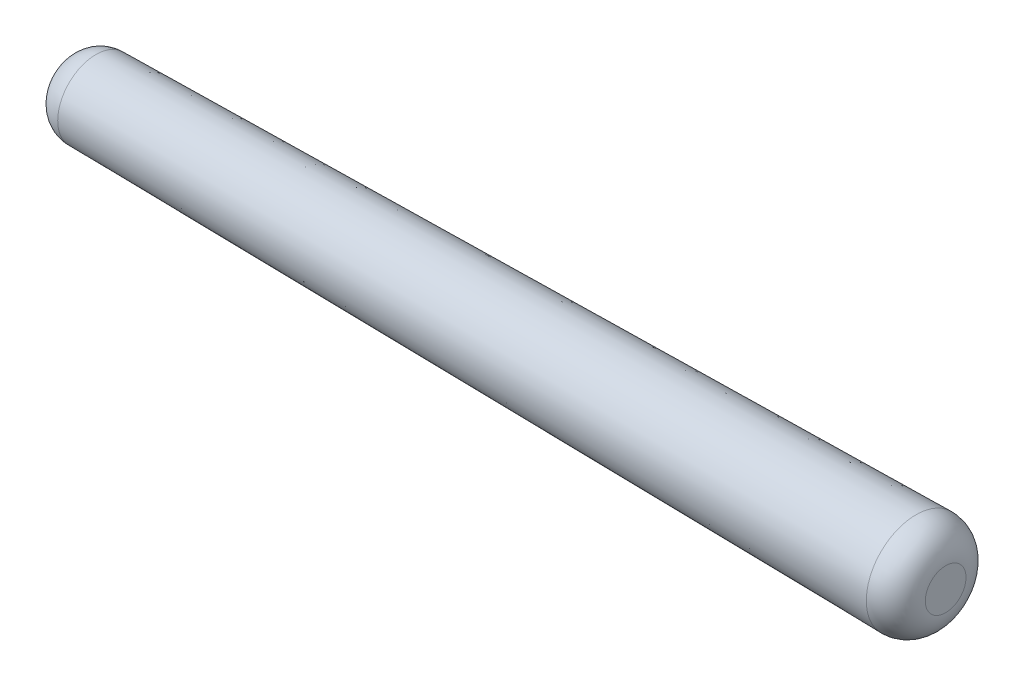
SolidWorks part; units mm, degrees
ref_plane "Front Plane" through (0, 0, 0) normal (0, 0, 1) x (1, 0, 0)
ref_plane "Top Plane" through (0, 0, 0) normal (0, 1, 0) x (1, 0, 0)
ref_plane "Right Plane" through (0, 0, 0) normal (1, 0, 0) x (0, 0, -1)
sketch "Sketch1" plane through (0, 0, 0) normal (1, 0, 0) x (0, 0, -1)
  circle A0 centre (0, 0) radius 0.6
  dimension "D1" = 1.2
sketch "Sketch2" plane through (0, 0, 0) normal (0, 0, 1) x (1, 0, 0)
  line L0 (6, 0) -> (-6, 0)
  line L1 (-6, -0.5162) -> (6, -0.6838)
  line L2 (6, -0.6838) -> (6, 0)
  line L3 (-6, 0) -> (-6, -0.5162)
  line L6 (0, -0.6) -> (0, 0.6) construction
  line L7 (0, -0.6) -> (0, 0.6) construction
  point P2 (0, 0)
  dimension "D1" = 12
  dimension "D2" = 0.8
revolve "Revolve1" add sketch "Sketch2" angle 360 about L0
fillet "Fillet1" radius 0.4 2 edges at (-6, 0.5162, 0) (6, 0.6838, 0)
